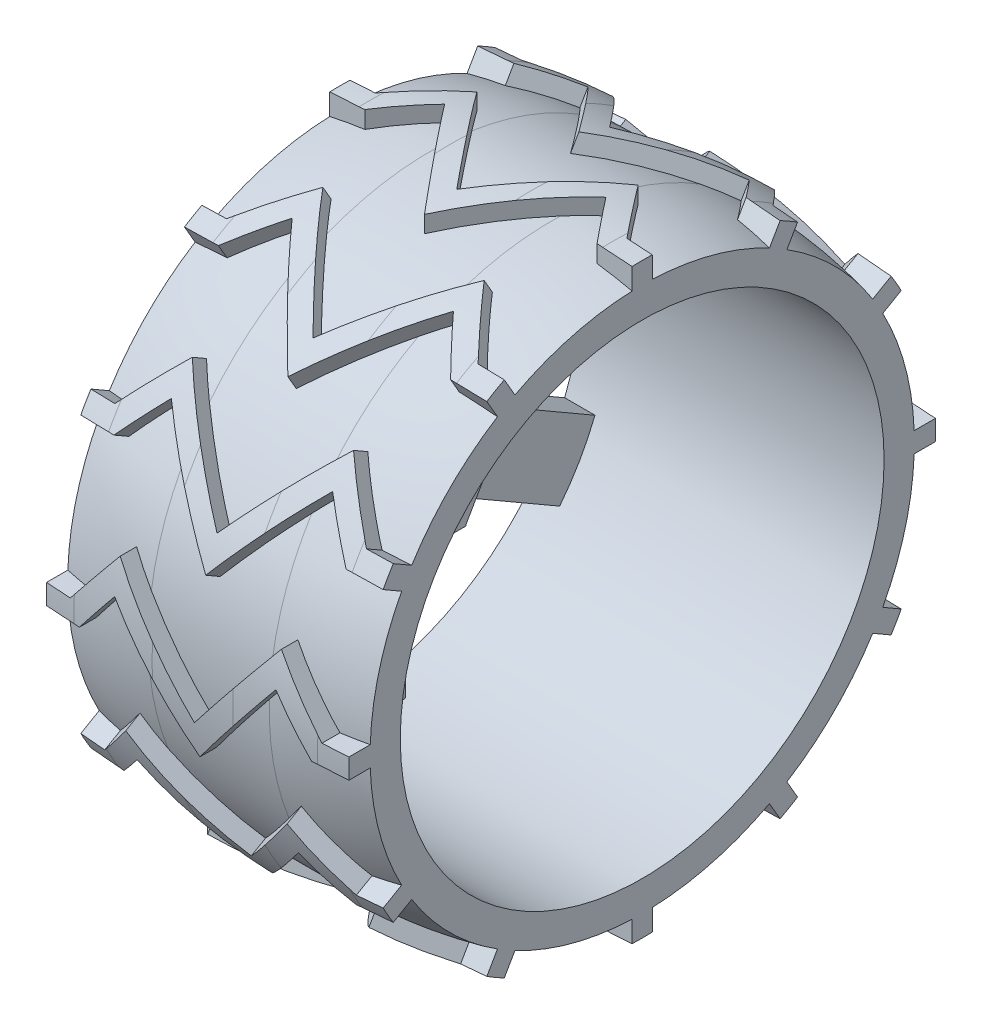
SolidWorks part; units mm, degrees
material "ABS"
ref_plane "Přední rovina" through (0, 0, 0) normal (0, 0, 1) x (1, 0, 0)
ref_plane "Horní rovina" through (0, 0, 0) normal (0, 1, 0) x (1, 0, 0)
ref_plane "Pravá rovina" through (0, 0, 0) normal (1, 0, 0) x (0, 0, -1)
sketch "Skica1" plane through (0, 0, 0) normal (0, 0, 1) x (1, 0, 0)
  line L0 (0, 0) -> (-19.9482, 0) construction
  line L1 (0, 0) -> (0, 24) construction
  line L2 (15, 24) -> (-15, 24)
  line L3 (-15, 24) -> (-15, 27)
  line L4 (0, 24) -> (0, 28) construction
  line L5 (6, 28) -> (-6, 28)
  line L6 (15, 24) -> (15, 27)
  arc A0 (-15, 27) -> (-6, 28) centre (-6, -13) cw
  arc A1 (15, 27) -> (6, 28) centre (6, -13) ccw
  dimension "D1" = 56
  dimension "D2" = 15
  dimension "D3" = 3
  dimension "D4" = 4
  dimension "D5" = 6
revolve "Rotovat1" add sketch "Skica1" angle 360 about L0
ref_plane "Rovina1" through (0, 30, 0) normal (0, 1, 0) x (1, 0, 0)
sketch "Skica3" plane through (0, 30, 0) normal (0, 1, 0) x (1, 0, 0)
  line L0 (-15, 0) -> (-12, 0)
  line L1 (-15, 27) -> (-15, -27) construction
  line L2 (-12, 0) -> (-8, 5)
  line L3 (-8, 5) -> (-4, 0)
  line L4 (0, 0) -> (-10.2838, 0) construction
  line L5 (0, 0) -> (0, -5) construction
  line L6 (-8, 5) -> (-8, 0) construction
  line L7 (-4, 0) -> (0, -5)
  line L8 (4, 0) -> (0, -5)
  line L9 (8, 5) -> (4, 0)
  line L10 (12, 0) -> (8, 5)
  line L11 (15, 0) -> (12, 0)
  dimension "D1" = 5
  dimension "D2" = 3
extrude "Vysunout tenkostěnný1" add sketch "Skica3" against normal blind 10 thin thin type mid plane wall 2
pattern_circular "Kruhové pole1" count 12 over 360 about axis through (0, 0, 0) along (1, 0, 0) of "Vysunout tenkostěnný1"
sketch "Skica4" plane through (0, 0, 0) normal (1, 0, 0) x (0, 0, -1)
  circle A0 centre (0, 0) radius 24
  circle A1 centre (0, 0) radius 27
  circle A2 centre (0, 0) radius 24 construction
  dimension "D1" = 3
extrude "Odebrat vysunutím2" cut sketch "Skica4" against normal mid plane 30 contours A0
sketch "Skica5" plane through (0, 0, 0) normal (1, 0, 0) x (0, 0, -1)
  circle A0 centre (0, 0) radius 30
  circle A1 centre (0, 0) radius 24 construction
  circle A2 centre (0, 0) radius 40
  dimension "D1" = 6
  dimension "D2" = 10
extrude "Odebrat vysunutím3" cut sketch "Skica5" against normal mid plane 30
sketch "Skica6" plane through (0, 0, 0) normal (0, 0, 1) x (1, 0, 0)
  line L0 (-15, 26.9815) -> (-15, 29.9833) construction
  line L1 (-2, 28.618) -> (-4, 28.618) construction
  line L2 (-2, 28.618) -> (4, 28.618) construction
  line L3 (-2, 29.618) -> (4, 29.618)
  line L4 (-2, 29.618) -> (-4, 29.618)
  line L5 (-15, 29.113) -> (-18.0891, 33.8325)
  line L6 (-18.0891, 33.8325) -> (1.0133, 32.6178)
  line L7 (1.0133, 32.6178) -> (17.1086, 33.5822)
  line L8 (17.1086, 33.5822) -> (15, 29.113)
  line L9 (0, 0) -> (-14.4667, 0) construction
  line L10 (15, 26.9815) -> (15, 29.9833) construction
  arc A4 (-12, 28.2983) -> (-14, 28.118) centre (-4, -71.632) ccw construction
  arc A5 (-4, 28.618) -> (-12, 28.2983) centre (-4, -71.632) ccw construction
  arc A6 (14, 28.118) -> (12, 28.2983) centre (4, -71.632) ccw construction
  arc A7 (12, 28.2983) -> (4, 28.618) centre (4, -71.632) ccw construction
  arc A8 (15, 29.113) -> (12.0798, 29.2951) centre (7.2394, -71.8391) ccw
  arc A9 (12.0798, 29.2951) -> (4, 29.618) centre (4, -71.632) ccw
  arc A10 (-4, 29.618) -> (-12.0798, 29.2951) centre (-4, -71.632) ccw
  arc A11 (-12.0798, 29.2951) -> (-15, 29.113) centre (-7.2394, -71.8391) ccw
revolve "Odebrat rotací1" cut sketch "Skica6" angle 360 about L9
sketch "Skica7" plane through (0, 0, 0) normal (0, 0, 1) x (1, 0, 0)
  line L0 (-6, 0) -> (-27.797, 0) construction
  line L1 (-15, 24) -> (-15, 13)
  line L2 (-15, 12.6247) -> (-15, 1) construction
  line L4 (-15, 13) -> (-15, 0)
  line L5 (-15, 0) -> (-6, 0)
  line L6 (-6, 0) -> (-6, 5.9654)
  line L7 (-6, 5.9654) -> (-12, 11)
  line L8 (-12, 11) -> (-12, 24)
  line L9 (-12, 24) -> (-15, 24)
  line L10 (-15, -1) -> (-15, -12.6247) construction
  dimension "D1" = 3
  dimension "D2" = 13
  dimension "D3" = 9
  dimension "D4" = 130
  dimension "D5" = 11
extrude "Přidat vysunutím1" add sketch "Skica7" along normal mid plane 7
pattern_circular "Kruhové pole2" count 6 over 360 about axis through (0, 0, 0) along (1, 0, 0) of "Přidat vysunutím1"
sketch "Skica9" plane through (-15, 0, 0) normal (-1, 0, 0) x (0, 0, 1)
  circle A0 centre (0, 0) radius 3.25
  dimension "D1" = 6.5
extrude "Odebrat vysunutím4" cut sketch "Skica9" against normal blind 4
sketch "Skica10" plane through (-11, 0, 0) normal (-1, 0, 0) x (0, 0, 1)
  circle A0 centre (0, 0) radius 1.4
  dimension "D1" = 2.8
extrude "Odebrat vysunutím5" cut sketch "Skica10" against normal blind 12
sketch "Skica11" plane through (-6, 0, 0) normal (1, 0, 0) x (0, 0, -1)
  circle A0 centre (0, 0) radius 2.75
  dimension "D1" = 5.5
extrude "Odebrat vysunutím6" [suppressed] cut sketch "Skica11" against normal blind 2.5
sketch "Skica12" plane through (-6, 0, 0) normal (1, 0, 0) x (0, 0, -1)
  line L24 (-3.4441, 5.9654) -> (-3.5, 5.9654)
  line L25 (-3.4441, 5.9654) -> (-3.5, 5.9654)
  line L26 (-6.8883, 0) -> (-6.9162, -0.0484)
  line L27 (-6.8883, 0) -> (-6.9162, -0.0484)
  line L28 (-3.4441, -5.9654) -> (-3.4162, -6.0138)
  line L29 (-3.4441, -5.9654) -> (-3.4162, -6.0138)
  line L30 (3.4441, -5.9654) -> (3.5, -5.9654)
  line L31 (-3.3324, 5.9654) -> (-3.4162, 6.0138)
  line L32 (-3.4162, 6.0138) -> (-3.4441, 5.9654)
  line L33 (3.4441, -5.9654) -> (3.5, -5.9654)
  line L34 (-3.5, 5.9654) -> (-3.5, 5.8686)
  line L35 (6.8883, 0) -> (6.9162, 0.0484)
  line L36 (-6.8324, 0.0968) -> (-6.9162, 0.0484)
  line L37 (-6.9162, 0.0484) -> (-6.8883, 0)
  line L38 (6.8883, 0) -> (6.9162, 0.0484)
  line L39 (-6.9162, -0.0484) -> (-6.8324, -0.0968)
  line L40 (3.5, 5.9654) -> (3.4441, 5.9654)
  line L41 (-3.5, -5.8686) -> (-3.5, -5.9654)
  line L42 (-3.5, -5.9654) -> (-3.4441, -5.9654)
  line L43 (3.5, 5.9654) -> (3.4441, 5.9654)
  line L44 (-3.4162, -6.0138) -> (-3.3324, -5.9654)
  line L45 (3.4441, 5.9654) -> (3.4162, 6.0138)
  line L46 (3.3324, -5.9654) -> (3.4162, -6.0138)
  line L47 (3.4162, -6.0138) -> (3.4441, -5.9654)
  line L48 (3.4441, 5.9654) -> (3.4162, 6.0138)
  line L49 (3.5, -5.9654) -> (3.5, -5.8686)
  line L51 (6.8324, -0.0968) -> (6.9162, -0.0484)
  line L52 (6.9162, -0.0484) -> (6.8883, 0)
  line L54 (6.9162, 0.0484) -> (6.8324, 0.0968)
  line L56 (3.5, 5.8686) -> (3.5, 5.9654)
  line L59 (3.4162, 6.0138) -> (3.3324, 5.9654)
  line L61 (-3.3324, 5.9654) -> (-3.4162, 6.0138)
  line L62 (-3.4162, 6.0138) -> (-3.4441, 5.9654)
  line L63 (3.3324, 5.9654) -> (-3.3324, 5.9654)
  line L64 (-3.5, 5.9654) -> (-3.5, 5.8686)
  line L65 (3.3324, 5.9654) -> (-3.3324, 5.9654)
  line L66 (-6.8324, 0.0968) -> (-6.9162, 0.0484)
  line L67 (-6.9162, 0.0484) -> (-6.8883, 0)
  line L68 (-3.5, 5.8686) -> (-6.8324, 0.0968)
  line L69 (-6.9162, -0.0484) -> (-6.8324, -0.0968)
  line L70 (-3.5, 5.8686) -> (-6.8324, 0.0968)
  line L71 (-3.5, -5.8686) -> (-3.5, -5.9654)
  line L72 (-3.5, -5.9654) -> (-3.4441, -5.9654)
  line L73 (-6.8324, -0.0968) -> (-3.5, -5.8686)
  line L74 (-3.4162, -6.0138) -> (-3.3324, -5.9654)
  line L75 (-6.8324, -0.0968) -> (-3.5, -5.8686)
  line L76 (3.3324, -5.9654) -> (3.4162, -6.0138)
  line L77 (3.4162, -6.0138) -> (3.4441, -5.9654)
  line L78 (-3.3324, -5.9654) -> (3.3324, -5.9654)
  line L79 (3.5, -5.9654) -> (3.5, -5.8686)
  line L80 (-3.3324, -5.9654) -> (3.3324, -5.9654)
  line L81 (6.8324, -0.0968) -> (6.9162, -0.0484)
  line L82 (6.9162, -0.0484) -> (6.8883, 0)
  line L83 (3.5, -5.8686) -> (6.8324, -0.0968)
  line L84 (6.9162, 0.0484) -> (6.8324, 0.0968)
  line L85 (3.5, -5.8686) -> (6.8324, -0.0968)
  line L86 (3.5, 5.8686) -> (3.5, 5.9654)
  line L87 (6.8324, 0.0968) -> (3.5, 5.8686)
  line L88 (6.8324, 0.0968) -> (3.5, 5.8686)
  line L89 (3.4162, 6.0138) -> (3.3324, 5.9654)
  circle A0 centre (0, 0) radius 7
  dimension "D1" = 0
extrude "Přidat vysunutím2" [suppressed] add sketch "Skica12" against normal up to next
sketch "Skica13" plane through (-6, 0, 0) normal (1, 0, 0) x (0, 0, -1)
  circle A0 centre (0, 0) radius 3.25
  dimension "D1" = 6.5
extrude "Odebrat vysunutím7" cut sketch "Skica13" against normal blind 2
